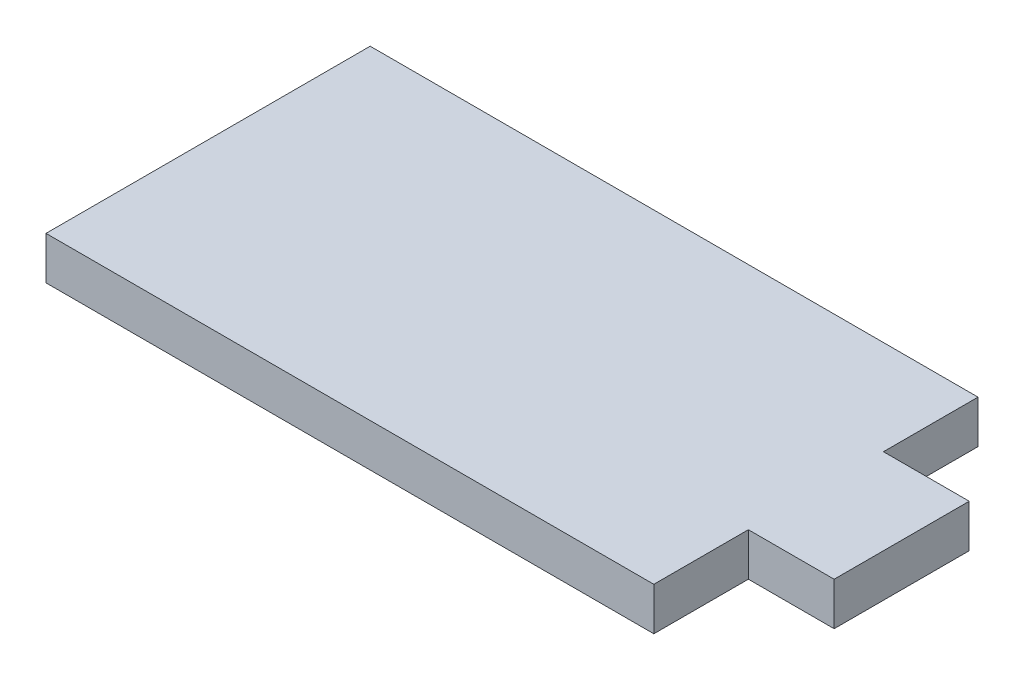
SolidWorks part; units mm, degrees
material "Cedar"
ref_plane "Front Plane" through (0, 0, 0) normal (0, 0, 1) x (1, 0, 0)
ref_plane "Top Plane" through (0, 0, 0) normal (0, 1, 0) x (1, 0, 0)
ref_plane "Right Plane" through (0, 0, 0) normal (1, 0, 0) x (0, 0, -1)
sketch "Sketch1" plane through (0, 0, 0) normal (0, 1, 0) x (1, 0, 0)
  line L0 (-22.5, 7) -> (22.5, 7)
  line L1 (22.5, 7) -> (22.5, 0)
  line L2 (22.5, 0) -> (28.85, 0)
  line L3 (28.85, 0) -> (28.85, -10)
  line L4 (28.85, -10) -> (22.5, -10)
  line L5 (22.5, -10) -> (22.5, -17)
  line L6 (22.5, -17) -> (-22.5, -17)
  line L7 (-22.5, -17) -> (-22.5, -10)
  line L8 (-22.5, -10) -> (-28.85, -10)
  line L9 (-28.85, -10) -> (-28.85, 0)
  line L10 (-28.85, 0) -> (-22.5, 0)
  line L11 (-22.5, 0) -> (-22.5, 7)
  line L12 (-22.5, 0) -> (-22.5, -10) construction
  point P11 (0, 7)
  point P14 (-28.85, -5)
  dimension "D1" = 6.35
  dimension "D2" = 10
  dimension "D3" = 45
  dimension "D4" = 24
extrude "Boss-Extrude1" add sketch "Sketch1" along normal blind 3.175 contours L11 L12 L7 L6 L5 L4 L3 L2 L1 L0
equation "\"length\"= 24mm"
equation "\"w_mach\"= 45mm"
equation "\"w_tab\"= 10mm"
equation "\"t_wood\"= 0.125in"
equation "\"t_side\"= 0.25in"
equation "\"D1@Sketch1\"=\"t_side\""
equation "\"D2@Sketch1\"=\"w_tab\""
equation "\"D3@Sketch1\"=\"w_mach\""
equation "\"D4@Sketch1\"=\"length\""
equation "\"D1@Boss-Extrude1\"=\"t_wood\""
